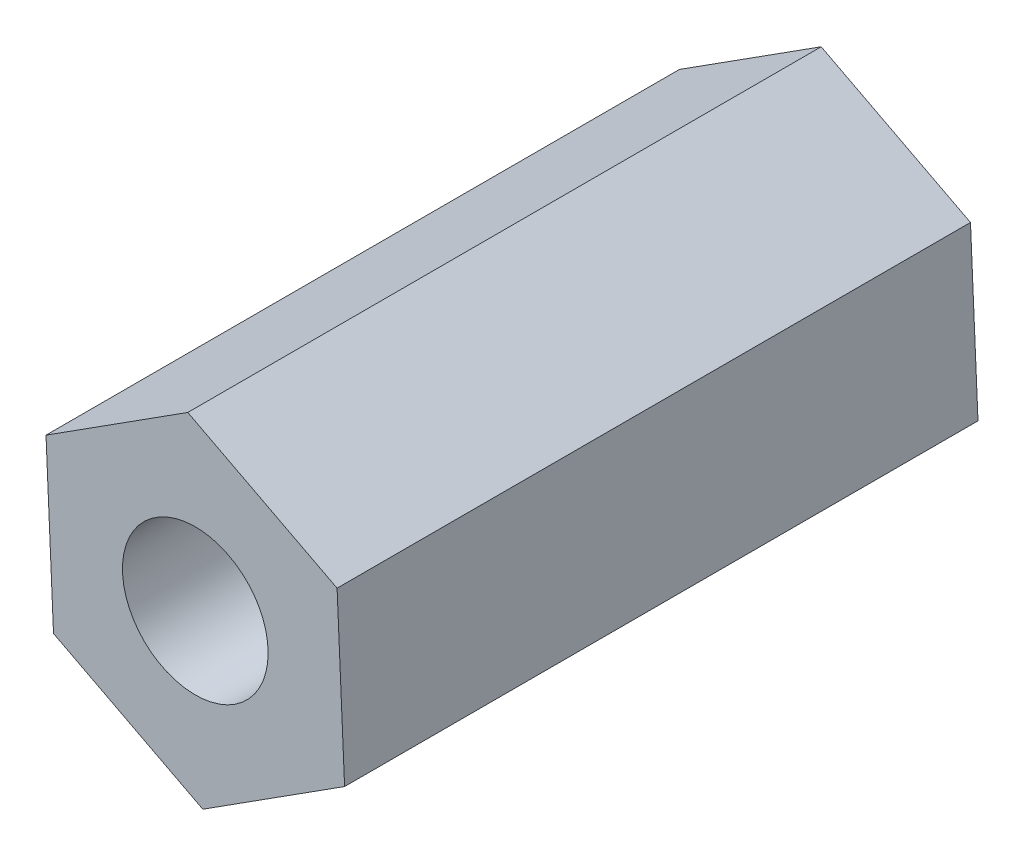
SolidWorks part; units mm, degrees
ref_plane "Front Plane" through (0, 0, 0) normal (0, 0, 1) x (1, 0, 0)
ref_plane "Top Plane" through (0, 0, 0) normal (0, 1, 0) x (1, 0, 0)
ref_plane "Right Plane" through (0, 0, 0) normal (1, 0, 0) x (0, 0, -1)
sketch "Sketch1" plane through (0, 0, 0) normal (0, 0, 1) x (1, 0, 0)
  line L1 (2.357, -1.2238) -> (2.2384, 1.4293)
  line L2 (2.2384, 1.4293) -> (-0.1186, 2.6532)
  line L3 (-0.1186, 2.6532) -> (-2.357, 1.2238)
  line L4 (-2.357, 1.2238) -> (-2.2384, -1.4293)
  line L5 (-2.2384, -1.4293) -> (0.1186, -2.6532)
  line L6 (0.1186, -2.6532) -> (2.357, -1.2238)
  circle A0 centre (0, 0) radius 2.3 construction
  circle A1 centre (0, 0) radius 1.15
extrude "Boss-Extrude1" add sketch "Sketch1" along normal blind 10
